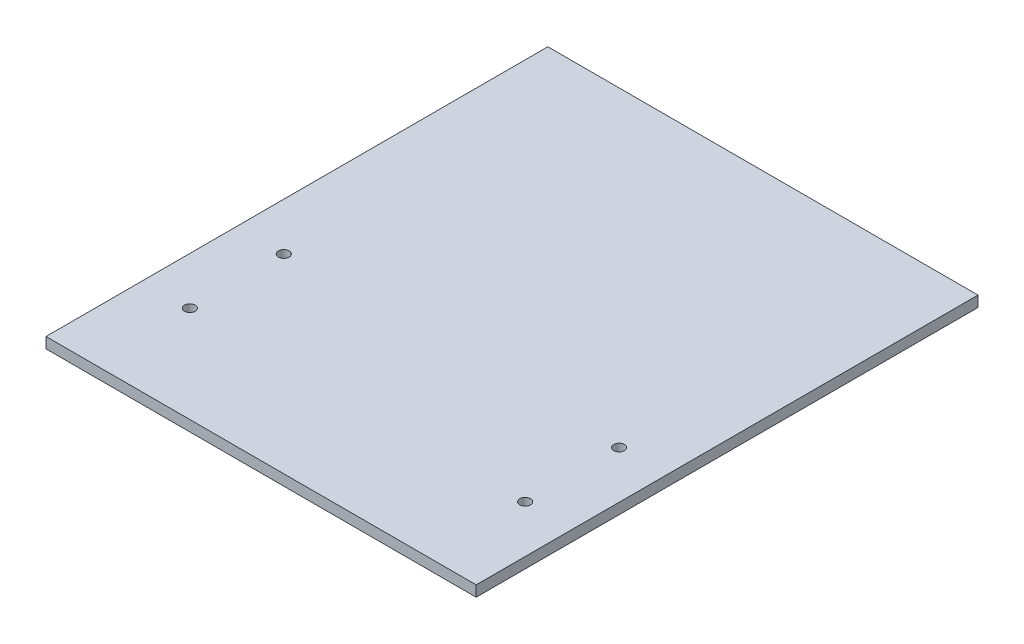
SolidWorks part; units mm, degrees
ref_plane "Front Plane" through (0, 0, 0) normal (0, 0, 1) x (1, 0, 0)
ref_plane "Top Plane" through (0, 0, 0) normal (0, 1, 0) x (1, 0, 0)
ref_plane "Right Plane" through (0, 0, 0) normal (1, 0, 0) x (0, 0, -1)
sketch "Sketch1" plane through (0, 0, 0) normal (0, 1, 0) x (1, 0, 0)
  line L1 (-60, -70) -> (60, -70)
  line L2 (-60, -70) -> (-60, 70)
  line L3 (-60, 70) -> (60, 70)
  line L4 (60, -70) -> (60, 70)
  line L5 (-60, -70) -> (60, 70) construction
  line L6 (-60, 70) -> (60, -70) construction
  point P0 (0, 0)
  dimension "D1" = 120
  dimension "D2" = 140
extrude "Boss-Extrude1" add sketch "Sketch1" along normal blind 3
sketch "Sketch2" plane through (0, 3, 0) normal (0, 1, 0) x (1, 0, 0)
  line L0 (-60, -30) -> (60, -30) construction
  line L1 (-60, 70) -> (-60, -70) construction
  line L2 (60, -70) -> (60, 70) construction
  line L3 (-46.7702, -6.2507) -> (-46.7702, -62.0916) construction
  line L4 (0, 70) -> (0, -70) construction
  line L5 (60, 70) -> (-60, 70) construction
  line L6 (-60, -70) -> (60, -70) construction
  line L7 (46.7702, -6.2507) -> (46.7702, -62.0916) construction
  circle A0 centre (-46.7702, -16.9) radius 1.5
  circle A1 centre (-46.7702, -43.1) radius 1.5
  circle A2 centre (46.7702, -43.1) radius 1.5
  circle A3 centre (46.7702, -16.9) radius 1.5
  dimension "D3" = 3
  dimension "D4" = 3
  dimension "D1" = 13.1
  dimension "D2" = 13.1
  dimension "D5" = 40
extrude "Cut-Extrude1" cut sketch "Sketch2" against normal through all
